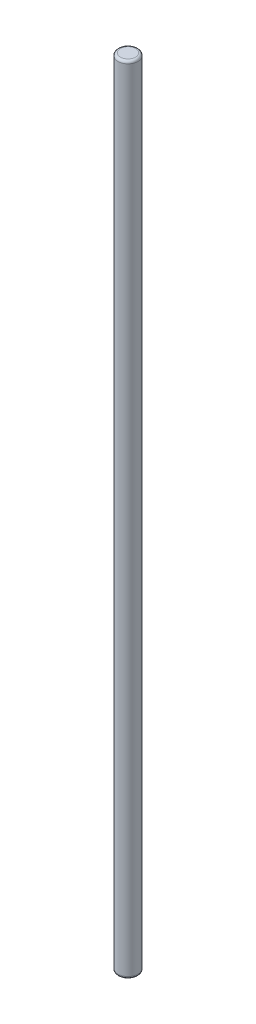
SolidWorks part; units mm, degrees
material "Chrome Stainless Steel"
ref_plane "Front Plane" through (0, 0, 0) normal (0, 0, 1) x (1, 0, 0)
ref_plane "Top Plane" through (0, 0, 0) normal (0, 1, 0) x (1, 0, 0)
ref_plane "Right Plane" through (0, 0, 0) normal (1, 0, 0) x (0, 0, -1)
sketch "Sketch1" plane through (0, 0, 0) normal (0, 1, 0) x (1, 0, 0)
  circle A0 centre (0, 0) radius 4
extrude "Boss-Extrude1" add sketch "Sketch1" along normal blind 317
fillet "Fillet2" radius 1 2 edges at (0, 0, 4) (0, 317, 4)
